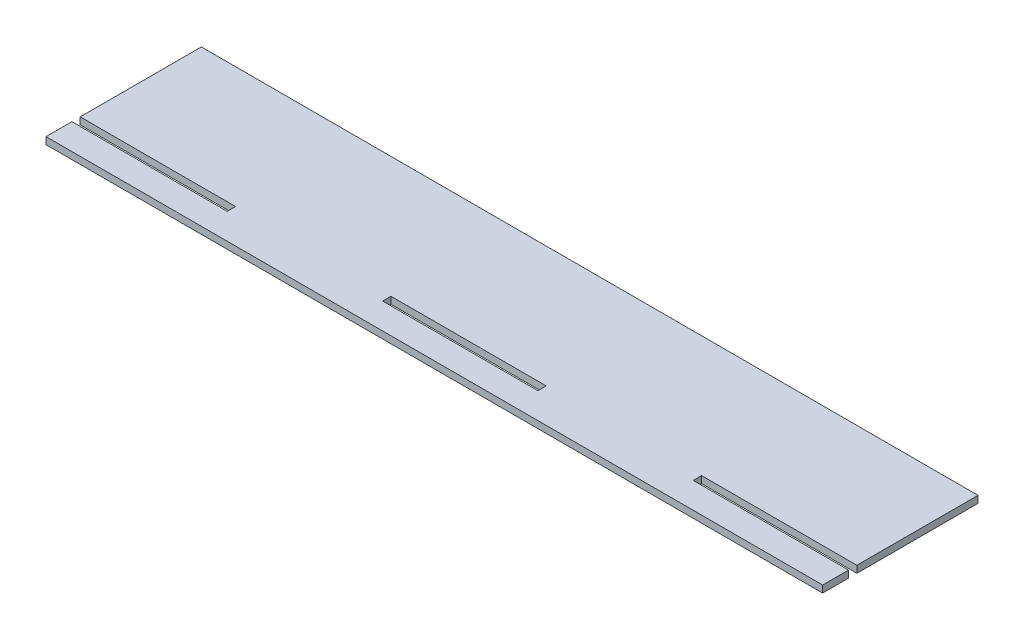
SolidWorks part; units mm, degrees
ref_plane "Front Plane" through (0, 0, 0) normal (0, 0, 1) x (1, 0, 0)
ref_plane "Top Plane" through (0, 0, 0) normal (0, 1, 0) x (1, 0, 0)
ref_plane "Right Plane" through (0, 0, 0) normal (1, 0, 0) x (0, 0, -1)
sketch "Sketch1" plane through (0, 0, 0) normal (0, 1, 0) x (1, 0, 0)
  line L0 (-150, -20) -> (-90, -20)
  line L1 (-150, 30) -> (150, 30)
  line L2 (-150, 30) -> (-150, -16.782)
  line L3 (-150, -30) -> (150, -30)
  line L4 (150, 30) -> (150, -16.782)
  line L5 (-150, -16.782) -> (-90, -16.782)
  line L6 (90, -20) -> (150, -20)
  line L7 (-30, -16.782) -> (30, -16.782)
  line L9 (90, -16.782) -> (150, -16.782)
  line L10 (-90, -16.782) -> (-90, -20)
  line L11 (-30, -16.782) -> (-30, -20)
  line L12 (30, -16.782) -> (30, -20)
  line L13 (90, -16.782) -> (90, -20)
  line L14 (-150, -20) -> (-150, -30)
  line L15 (-30, -20) -> (30, -20)
  line L16 (150, -20) -> (150, -30)
  point P0 (0, 0)
  dimension "D1" = 300
  dimension "D2" = 60
  dimension "D3" = 10
  dimension "D4" = 3.218
extrude "Boss-Extrude1" add sketch "Sketch1" along normal blind 2.7
